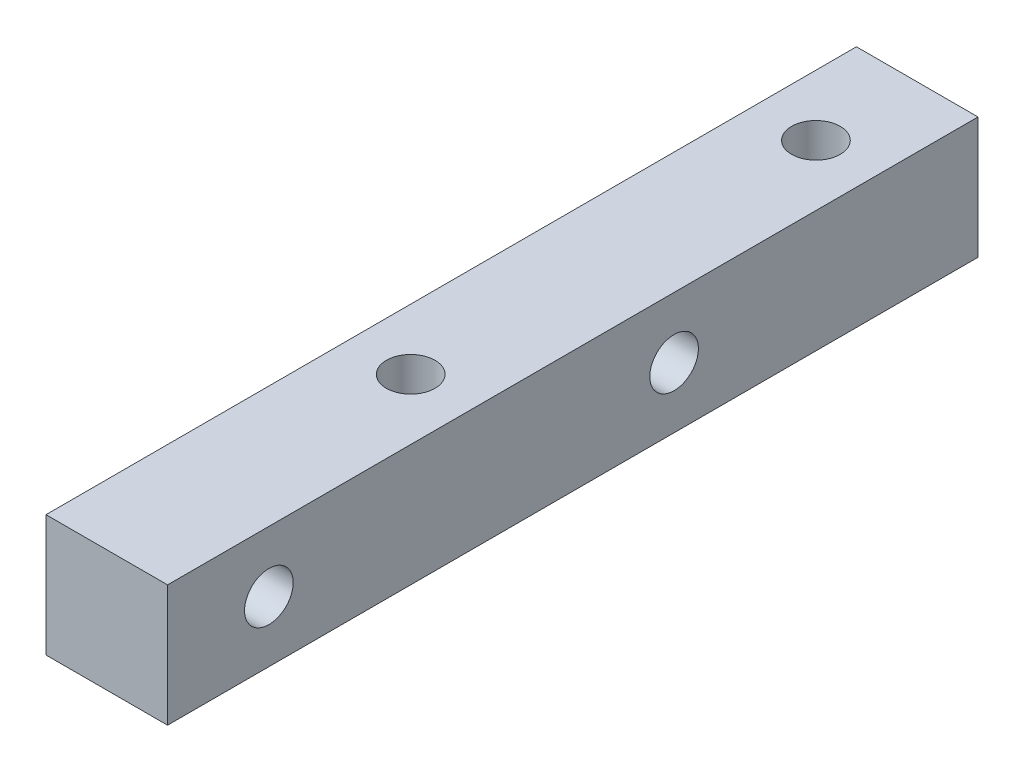
SolidWorks part; units mm, degrees
material "6061-T6 (SS)"
ref_plane "前视基准面" through (0, 0, 0) normal (0, 0, 1) x (1, 0, 0)
ref_plane "上视基准面" through (0, 0, 0) normal (0, 1, 0) x (1, 0, 0)
ref_plane "右视基准面" through (0, 0, 0) normal (1, 0, 0) x (0, 0, -1)
sketch "草图1" plane through (0, 0, 0) normal (0, 0, 1) x (1, 0, 0)
  line L1 (0, 0) -> (6, 0)
  line L2 (0, 0) -> (0, 6)
  line L3 (0, 6) -> (6, 6)
  line L4 (6, 0) -> (6, 6)
  dimension "D1" = 6
  dimension "D2" = 6
extrude "凸台-拉伸1" add sketch "草图1" along normal blind 40
sketch "草图2" plane through (0, 6, 0) normal (0, 1, 0) x (1, 0, 0)
  line L0 (3, 0) -> (3, -5) construction
  line L1 (6, 0) -> (0, 0) construction
  line L2 (3, -5) -> (3, -25) construction
  circle A0 centre (3, -5) radius 1.2
  circle A1 centre (3, -25) radius 1.2
  dimension "D1" = 2.4
  dimension "D2" = 5
  dimension "D3" = 20
extrude "切除-拉伸1" cut sketch "草图2" against normal blind 50
cosmetic thread "装饰螺纹线5"
cosmetic thread "装饰螺纹线6"
sketch "草图3" plane through (0, 0, 0) normal (-1, 0, 0) x (0, 0, 1)
  line L0 (0, 3) -> (15, 3) construction
  line L1 (0, 6) -> (0, 0) construction
  line L2 (15, 3) -> (35, 3) construction
  circle A0 centre (35, 3) radius 1.2
  circle A1 centre (15, 3) radius 1.2
  dimension "D3" = 2.4
  dimension "D1" = 15
  dimension "D2" = 20
extrude "切除-拉伸2" cut sketch "草图3" against normal blind 50
cosmetic thread "装饰螺纹线7" parameters "D2"=3
cosmetic thread "装饰螺纹线8" parameters "D2"=3
